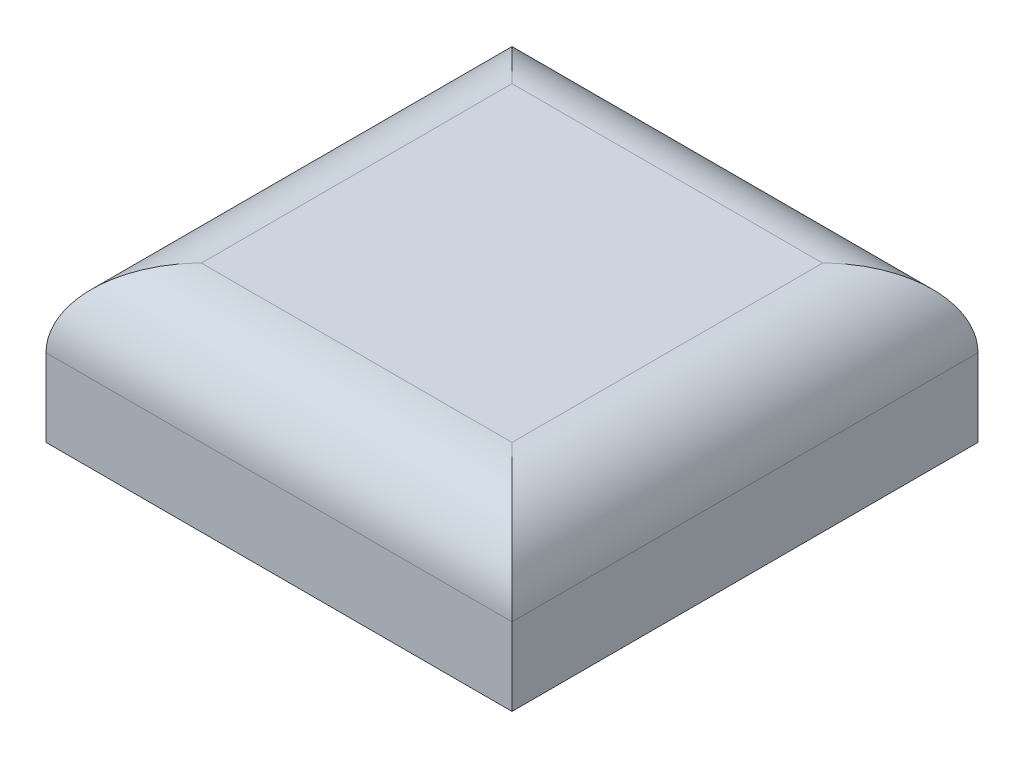
SolidWorks part; units mm, degrees
ref_plane "Front Plane" through (0, 0, 0) normal (0, 0, 1) x (1, 0, 0)
ref_plane "Top Plane" through (0, 0, 0) normal (0, 1, 0) x (1, 0, 0)
ref_plane "Right Plane" through (0, 0, 0) normal (1, 0, 0) x (0, 0, -1)
sketch "Sketch1" plane through (0, 0, 0) normal (0, 1, 0) x (1, 0, 0)
  line L1 (-15.0231, 8.3308) -> (-3.0231, 8.3308)
  line L2 (-15.0231, 8.3308) -> (-15.0231, -3.6692)
  line L3 (-15.0231, -3.6692) -> (-3.0231, -3.6692)
  line L4 (-3.0231, 8.3308) -> (-3.0231, -3.6692)
  line L5 (-15.0231, 8.3308) -> (-3.0231, -3.6692) construction
  line L6 (-15.0231, -3.6692) -> (-3.0231, 8.3308) construction
  point P0 (-9.0231, 2.3308)
  dimension "D1" = 12
  dimension "D2" = 12
extrude "Boss-Extrude1" add sketch "Sketch1" along normal blind 4
sketch "Sketch2" plane through (0, 0, 0) normal (0, -1, 0) x (1, 0, 0)
  line L0 (-3.0231, 3.6692) -> (-15.0231, -8.3308) construction
  circle A0 centre (-9.0231, -2.3308) radius 2
extrude "Cut-Extrude1" cut sketch "Sketch2" against normal blind 2
fillet "Fillet1" radius 2 4 edges at (-9.0231, 4, -8.3308) (-3.0231, 4, -2.3308) (-9.0231, 4, 3.6692) (-15.0231, 4, -2.3308)
